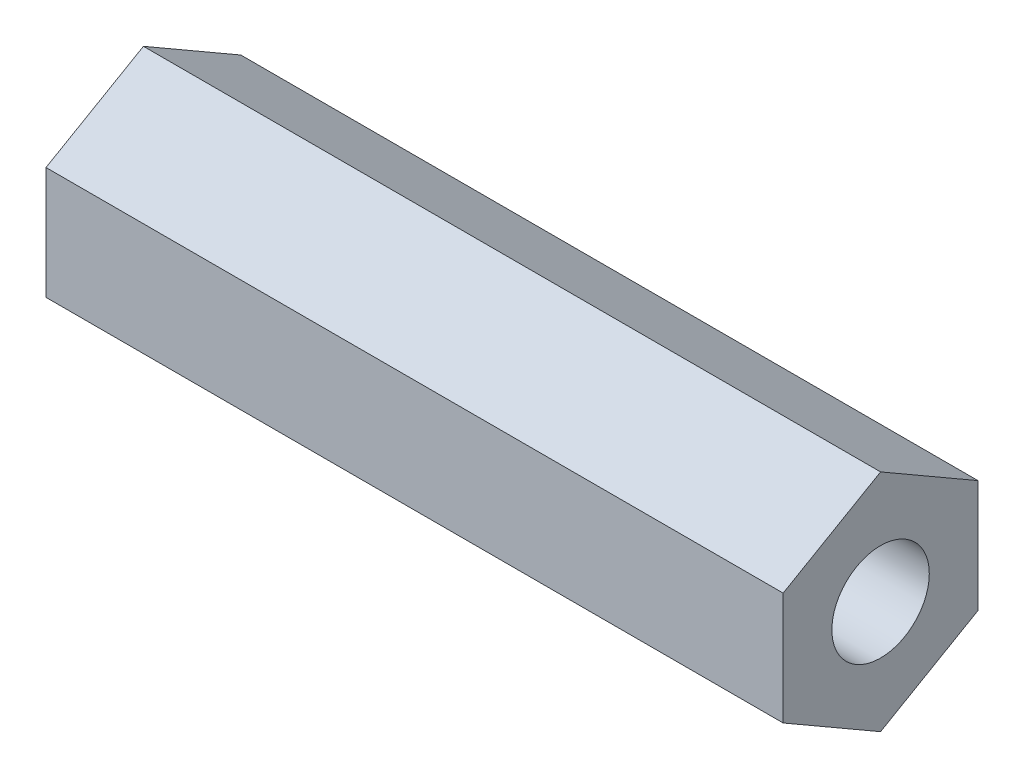
SolidWorks part; units mm, degrees
ref_plane "Front Plane" through (0, 0, 0) normal (0, 0, 1) x (1, 0, 0)
ref_plane "Top Plane" through (0, 0, 0) normal (0, 1, 0) x (1, 0, 0)
ref_plane "Right Plane" through (0, 0, 0) normal (1, 0, 0) x (0, 0, -1)
sketch "Sketch1" plane through (0, 0, 0) normal (1, 0, 0) x (0, 0, -1)
  line L7 (-42.7283, 8.2771) -> (-45.7283, 6.5451)
  line L8 (-45.7283, 6.5451) -> (-45.7283, 3.081)
  line L9 (-45.7283, 3.081) -> (-42.7283, 1.3489)
  line L10 (-42.7283, 1.3489) -> (-39.7283, 3.081)
  line L11 (-39.7283, 3.081) -> (-39.7283, 6.5451)
  line L12 (-39.7283, 6.5451) -> (-42.7283, 8.2771)
  circle A0 centre (-42.7283, 4.813) radius 1.5
  circle A2 centre (-42.7283, 4.813) radius 3 construction
  dimension "D1" = 3
extrude "Boss-Extrude1" add sketch "Sketch1" along normal blind 22.7
